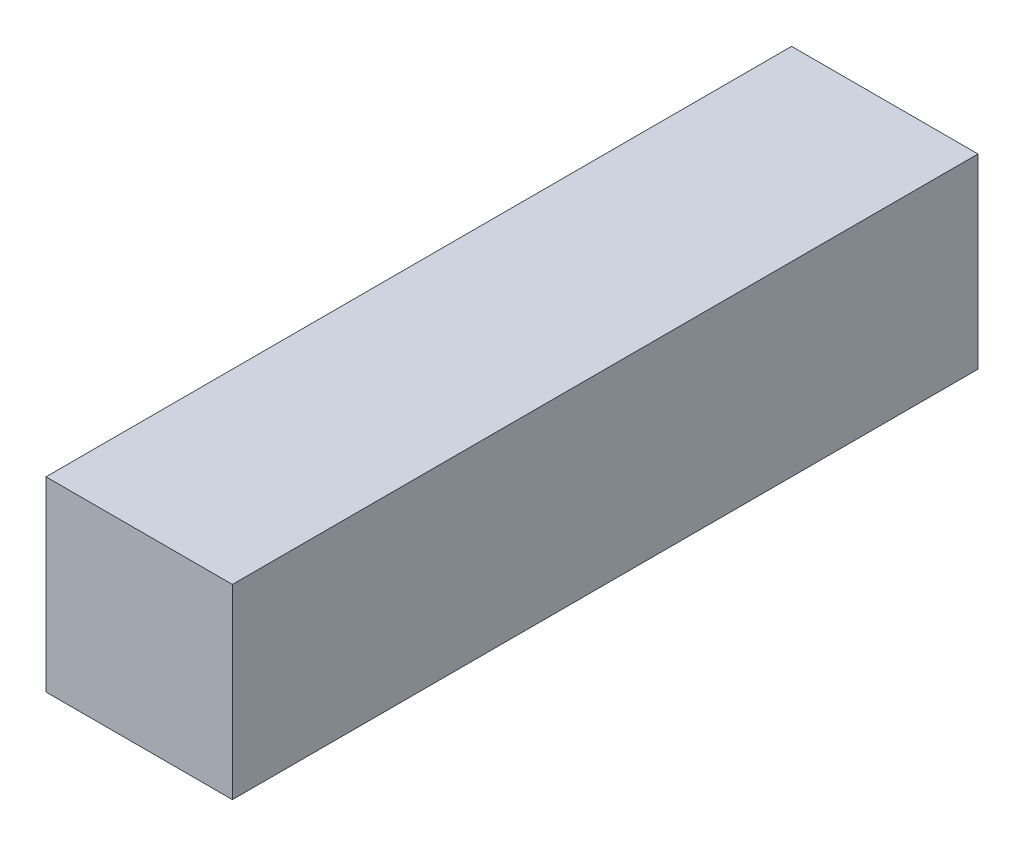
SolidWorks part; units mm, degrees
ref_plane "Front Plane" through (0, 0, 0) normal (0, 0, 1) x (1, 0, 0)
ref_plane "Top Plane" through (0, 0, 0) normal (0, 1, 0) x (1, 0, 0)
ref_plane "Right Plane" through (0, 0, 0) normal (1, 0, 0) x (0, 0, -1)
sketch "Sketch1" plane through (0, 0, 0) normal (0, 1, 0) x (1, 0, 0)
  line L1 (-2500, -10000) -> (2500, -10000)
  line L2 (-2500, -10000) -> (-2500, 10000)
  line L3 (-2500, 10000) -> (2500, 10000)
  line L4 (2500, -10000) -> (2500, 10000)
  line L5 (-2500, -10000) -> (2500, 10000) construction
  line L6 (-2500, 10000) -> (2500, -10000) construction
  point P0 (0, 0)
  dimension "D1" = 5000
  dimension "D2" = 20000
extrude "Boss-Extrude1" add sketch "Sketch1" along normal blind 5000 contours L2 L1 L4 L3
